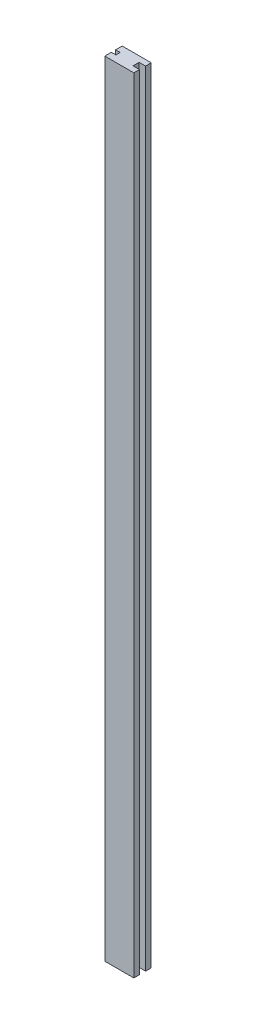
SolidWorks part; units mm, degrees
ref_plane "Спереди" through (0, 0, 0) normal (0, 0, 1) x (1, 0, 0)
ref_plane "Сверху" through (0, 0, 0) normal (0, 1, 0) x (1, 0, 0)
ref_plane "Справа" through (0, 0, 0) normal (1, 0, 0) x (0, 0, -1)
sketch "Эскиз1" plane through (0, 0, 0) normal (0, 1, 0) x (1, 0, 0)
  line L0 (0, 3.6577) -> (0, -3.6577)
  line L1 (0, -3.6577) -> (-7.957, -3.6577)
  line L2 (-7.957, -3.6577) -> (-7.957, -15)
  line L3 (-7.957, -15) -> (42.043, -15)
  line L4 (42.043, -15) -> (42.043, -5.25)
  line L5 (42.043, -5.25) -> (31, -5.25)
  line L6 (31, -5.25) -> (31, 0)
  line L7 (-18.9883, 0) -> (46.2952, 0) construction
  line L11 (31, 5.25) -> (31, 0)
  line L12 (42.043, 5.25) -> (31, 5.25)
  line L13 (42.043, 15) -> (42.043, 5.25)
  line L14 (-7.957, 15) -> (42.043, 15)
  line L15 (-7.957, 3.6577) -> (-7.957, 15)
  line L16 (0, 3.6577) -> (-7.957, 3.6577)
  point P21 (0, 0)
extrude "Бобышка-Вытянуть1" add sketch "Эскиз1" along normal blind 1350
